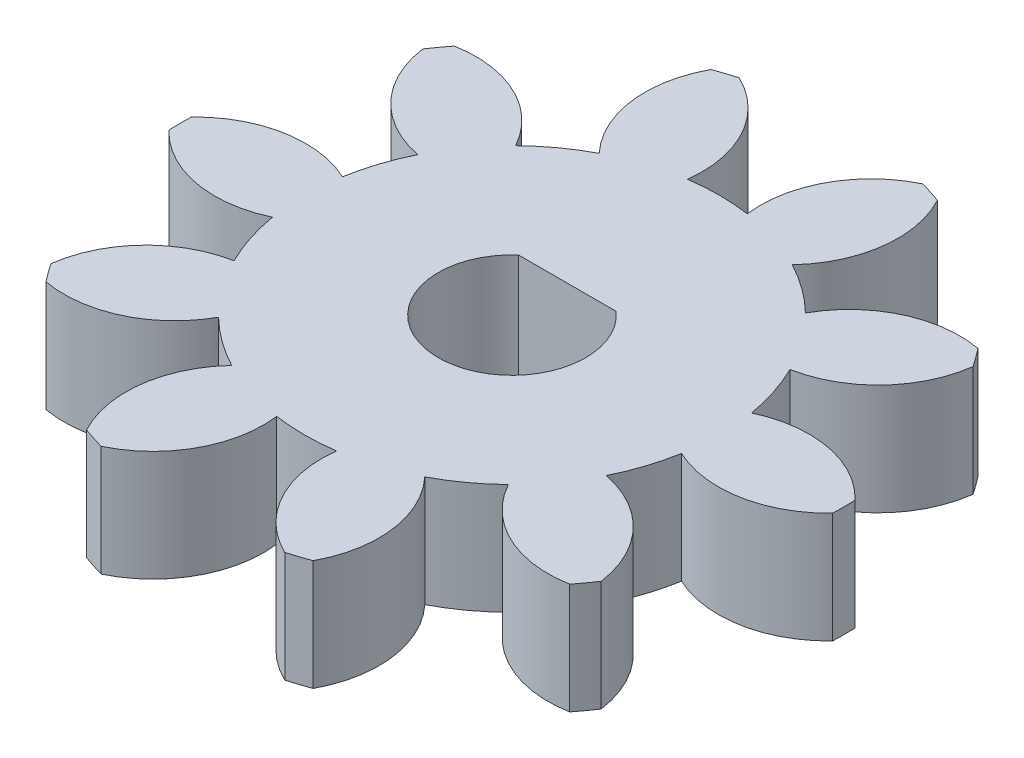
SolidWorks part; units mm, degrees
ref_plane "Front Plane" through (0, 0, 0) normal (0, 0, 1) x (1, 0, 0)
ref_plane "Top Plane" through (0, 0, 0) normal (0, 1, 0) x (1, 0, 0)
ref_plane "Right Plane" through (0, 0, 0) normal (1, 0, 0) x (0, 0, -1)
sketch "Sketch1" plane through (0, 0, 0) normal (0, 1, 0) x (1, 0, 0)
  circle A0 centre (0, 0) radius 9
  dimension "addendumDiamteter" = 18
extrude "Boss-Extrude1" add sketch "Sketch1" along normal blind 3
sketch "Sketch2" plane through (0, 3, 0) normal (0, 1, 0) x (1, 0, 0)
  line L0 (0, 0) -> (0, 28.8712) construction
  line L1 (0, 0) -> (-5.469, 16.832) construction
  line L3 (-1.1684, 7.4084) -> (-2.2889, 7.0444) construction
  circle A0 centre (0, 0) radius 7.5 construction
  circle A2 centre (0, 0) radius 5.625 construction
  circle A3 centre (0, 0) radius 7.0477 construction
  arc A4 (-0.8106, 5.5663) -> (0.8106, 5.5663) centre (0, 0) cw
  arc A5 (-2.4893, 8.6489) -> (2.4893, 8.6489) centre (0, 0) cw
  circle A6 centre (0, 0) radius 9 construction
  arc A7 (-2.4893, 8.6489) -> (-0.8106, 5.5663) centre (-3.7867, 5.944) cw
  arc A8 (2.4893, 8.6489) -> (0.8106, 5.5663) centre (3.7867, 5.944) ccw
  dimension "dedendumCircle" = 11.25
  dimension "baseDiameter" = 14.0954
  dimension "PitchDiameter" = 15
  dimension "D1" = 3
  dimension "D4" = 18
  dimension "D2" = 1.1781
extrude "Cut-Extrude1" cut sketch "Sketch2" against normal through all
pattern_circular "CirPattern1" count 10 over 360 about axis through (0, 0, 0) along (0, 1, 0) of "Cut-Extrude1"
sketch "Sketch3" [suppressed] plane through (0, 3, 0) normal (0, 1, 0) x (1, 0, 0)
  line L0 (0, 4) -> (-6.8829, 13.8298)
  line L2 (6.8829, 13.8298) -> (0, 4)
  line L3 (0, 0) -> (0, 31.2074) construction
  line L4 (0, 0) -> (46.4667, 0) construction
  line L5 (-6.8829, 13.8298) -> (6.8829, 13.8298) construction
  arc A0 (-6.8829, 13.8298) -> (6.8829, 13.8298) centre (0, 4) cw
  dimension "D4" = 12
  dimension "D1" = 75
  dimension "D2" = 5
  dimension "D3" = 11
extrude "Cut-Extrude2" [suppressed] cut sketch "Sketch3" against normal blind 10
fillet "Fillet1" [suppressed] radius 1
fillet "Fillet2" [suppressed] radius 1
fillet "Fillet3" [suppressed] radius 1
pattern_circular "CirPattern2" [suppressed] count 6 over 360
sketch "Sketch6" plane through (0, 3, 0) normal (0, 1, 0) x (1, 0, 0)
  line L0 (0, 0) -> (22.423, 0) construction
  line L1 (22.423, 0) -> (0, 0) construction
  line L2 (0, 0) -> (0, 27.3259) construction
  line L3 (1.3229, 1.5) -> (-1.3229, 1.5)
  arc A0 (-1.3229, 1.5) -> (1.3229, 1.5) centre (0, 0) ccw
  dimension "D1" = 2
  dimension "D2" = 1.5
extrude "Cut-Extrude5" cut sketch "Sketch6" against normal through all
equation "\"module\"= 1.5"
equation "\"teeth\"= 10"
equation "\"pressureAngle\"= 20deg"
equation "\"gearThickness\"= 3"
equation "\"addendumFactor\"= 1"
equation "\"dedendumFactor\"= 1.25"
equation "\"pitch\"= 1 / \"module\""
equation "\"pitchDiameter\"= \"teeth\" / \"pitch\""
equation "\"addendum\"= \"addendumFactor\" / \"pitch\""
equation "\"dedendum\"= \"dedendumFactor\" / \"pitch\""
equation "\"addendumDiamteter@Sketch1\"=\"pitchDiameter\"+(\"addendum\"*2)"
equation "\"dedendumCircle@Sketch2\"=\"pitchDiameter\" -2 *\"dedendum\""
equation "\"baseDiameter@Sketch2\"=\"pitchDiameter\"*cos( \"pressureAngle\")"
equation "\"PitchDiameter@Sketch2\"=\"pitchDiameter\""
equation "\"D4@Sketch2\"=180/\"teeth\""
equation "\"D1@Sketch2\"=\"pitchDiameter\"/5"
equation "\"D2@Sketch2\"=PI / 2 / \"pitch\" / 2"
equation "\"D1@CirPattern1\"=\"teeth\""
